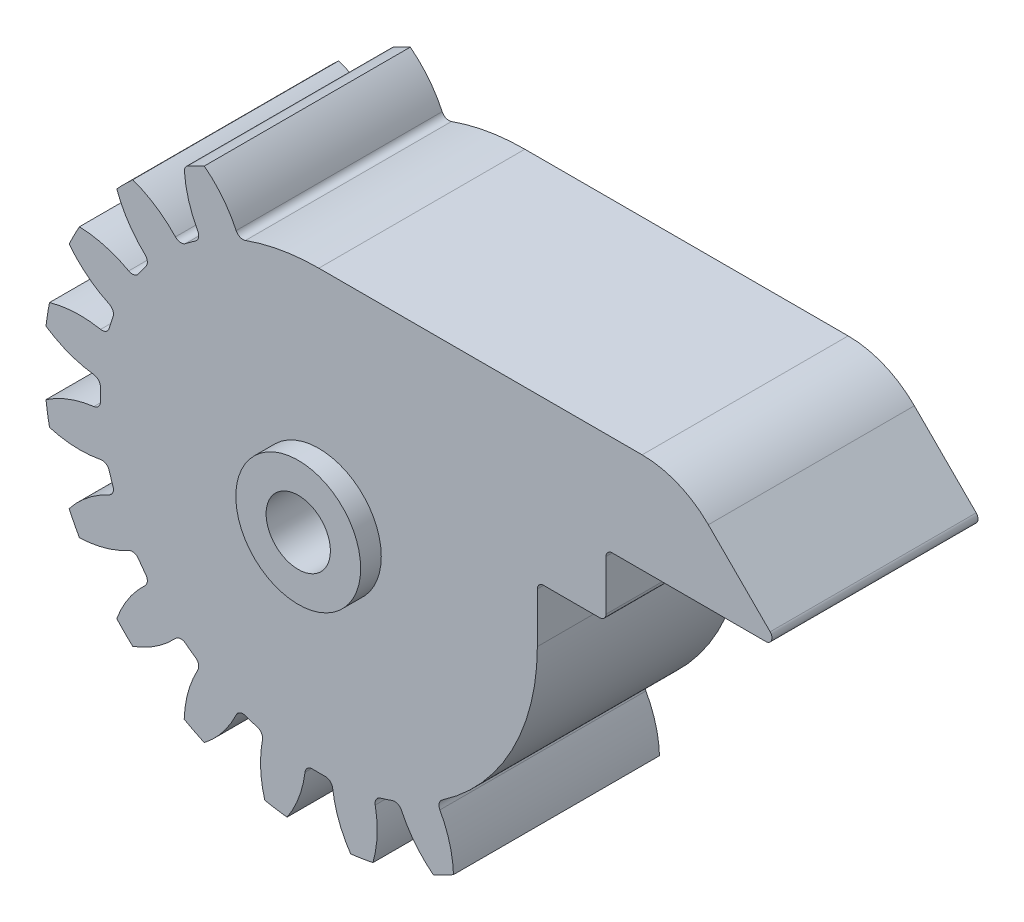
SolidWorks part; units mm, degrees
material "1023 Carbon Steel Sheet (SS)"
ref_plane "Front Plane" through (0, 0, 0) normal (0, 0, 1) x (1, 0, 0)
ref_plane "Top Plane" through (0, 0, 0) normal (0, 1, 0) x (1, 0, 0)
ref_plane "Right Plane" through (0, 0, 0) normal (1, 0, 0) x (0, 0, -1)
sketch "skBase" plane through (0, 0, 0) normal (0, 0, 1) x (1, 0, 0)
  circle A0 centre (0, 0) radius 20
  circle A1 centre (0, 0) radius 22
  circle A2 centre (0, 0) radius 17.5
  dimension "D1" = 40
  dimension "D3" = 4.5
extrude "Base" add sketch "skBase" along normal mid plane 16.5 contours A1
sketch "skToothProfile" plane through (0, 0, 0) normal (0, 0, 1) x (1, 0, 0)
  line L0 (0, 0) -> (0, 22) construction
  line L1 (-1.5692, 19.9383) -> (1.5692, 19.9383) construction
  line L2 (-1.0563, 17.4681) -> (0, 0) construction
  line L3 (0, 15.6271) -> (-2.6287, 22.8493) construction
  line L4 (0, 0) -> (3.4416, 21.7291) construction
  line L5 (1.5692, 19.9383) -> (4.6689, 19.4474) construction
  circle A0 centre (0, 0) radius 22 construction
  arc A1 (-1.0563, 17.4681) -> (-3.258, 22.7681) centre (-9.8105, 16.9387) ccw
  arc A2 (1.0563, 17.4681) -> (3.258, 22.7681) centre (9.8105, 16.9387) cw
  circle A3 centre (0, 0) radius 17.5 construction
  arc A4 (1.0563, 17.4681) -> (-1.0563, 17.4681) centre (0, 0) ccw
  circle A5 centre (0, 0) radius 20 construction
  circle A6 centre (0, 0) radius 22 construction
  circle A7 centre (0, 0) radius 23
  arc A8 (3.258, 22.7681) -> (-3.258, 22.7681) centre (0, 0) ccw
  dimension "D2" = 20
  dimension "D3" = 9
  dimension "D1" = 1
extrude "ToothProfile" cut sketch "skToothProfile" against normal through all and the other way through all
fillet "FilletToothProfile" radius 0.6 2 edges at (1.0563, 17.4681, 0) (-1.0563, 17.4681, 0)
pattern_circular "CirPatternTeeth" count 20 over 360 about axis through (0, 0, 0) along (0, 0, 1) of "ToothProfile", "FilletToothProfile"
sketch "skChaveta" plane through (0, 0, 8.25) normal (0, 0, 1) x (1, 0, 0)
  line L0 (0, 2.575) -> (0, 0) construction
  circle A0 centre (0, 0) radius 2.575
  dimension "D1" = 5.15
extrude "Chaveta" cut sketch "skChaveta" against normal through all
sketch "skRebaixo" plane through (0, 0, 8.25) normal (0, 0, 1) x (1, 0, 0)
  circle A0 centre (0, 0) radius 21.5
  circle A1 centre (0, 0) radius 7.5
  dimension "D1" = 43
  dimension "D2" = 15
sketch "Sketch4" plane through (0, 0, -8.25) normal (0, 0, -1) x (-1, 0, 0)
  circle A0 centre (0, 0) radius 17.5
  arc A5 (-2.5459, 21.8522) -> (-4.3314, 21.5694) centre (0, 0) ccw
  arc A6 (-2.5459, 21.8522) -> (-4.3314, 21.5694) centre (0, 0) ccw
  arc A7 (-18.0189, -1.107) -> (-21.8522, -2.5459) centre (-16.9387, -9.8105) ccw
  arc A8 (-18.0189, -1.107) -> (-21.8522, -2.5459) centre (-16.9387, -9.8105) ccw
  arc A9 (-21.5694, -4.3314) -> (-17.4791, -4.5153) centre (-19.1413, 4.096) ccw
  arc A10 (-21.5694, -4.3314) -> (-17.4791, -4.5153) centre (-19.1413, 4.096) ccw
  arc A127 (-19.996, -9.174) -> (-19.1752, -10.7848) centre (0, 0) ccw
  arc A128 (-19.996, -9.174) -> (-19.1752, -10.7848) centre (0, 0) ccw
  arc A129 (-16.1824, -14.904) -> (-14.904, -16.1824) centre (0, 0) ccw
  arc A130 (-16.1824, -14.904) -> (-14.904, -16.1824) centre (0, 0) ccw
  arc A131 (-10.7848, -19.1752) -> (-9.174, -19.996) centre (0, 0) ccw
  arc A132 (-10.7848, -19.1752) -> (-9.174, -19.996) centre (0, 0) ccw
  arc A133 (-4.3314, -21.5694) -> (-2.5459, -21.8522) centre (0, 0) ccw
  arc A134 (-4.3314, -21.5694) -> (-2.5459, -21.8522) centre (0, 0) ccw
  arc A135 (2.5459, -21.8522) -> (4.3314, -21.5694) centre (0, 0) ccw
  arc A136 (2.5459, -21.8522) -> (4.3314, -21.5694) centre (0, 0) ccw
  arc A137 (9.174, -19.996) -> (10.7848, -19.1752) centre (0, 0) ccw
  arc A138 (9.174, -19.996) -> (10.7848, -19.1752) centre (0, 0) ccw
  arc A139 (14.904, -16.1824) -> (16.1824, -14.904) centre (0, 0) ccw
  arc A140 (14.904, -16.1824) -> (16.1824, -14.904) centre (0, 0) ccw
  arc A141 (19.1752, -10.7848) -> (19.996, -9.174) centre (0, 0) ccw
  arc A142 (19.1752, -10.7848) -> (19.996, -9.174) centre (0, 0) ccw
  arc A143 (21.5694, -4.3314) -> (21.8522, -2.5459) centre (0, 0) ccw
  arc A144 (21.5694, -4.3314) -> (21.8522, -2.5459) centre (0, 0) ccw
  arc A145 (21.8522, 2.5459) -> (21.5694, 4.3314) centre (0, 0) ccw
  arc A146 (21.8522, 2.5459) -> (21.5694, 4.3314) centre (0, 0) ccw
  arc A147 (19.996, 9.174) -> (19.1752, 10.7848) centre (0, 0) ccw
  arc A148 (19.996, 9.174) -> (19.1752, 10.7848) centre (0, 0) ccw
  arc A149 (16.1824, 14.904) -> (14.904, 16.1824) centre (0, 0) ccw
  arc A150 (16.1824, 14.904) -> (14.904, 16.1824) centre (0, 0) ccw
  arc A151 (10.7848, 19.1752) -> (9.174, 19.996) centre (0, 0) ccw
  arc A152 (10.7848, 19.1752) -> (9.174, 19.996) centre (0, 0) ccw
  arc A153 (4.3314, 21.5694) -> (2.5459, 21.8522) centre (0, 0) ccw
  arc A154 (4.3314, 21.5694) -> (2.5459, 21.8522) centre (0, 0) ccw
  arc A155 (-9.174, 19.996) -> (-10.7848, 19.1752) centre (0, 0) ccw
  arc A156 (-9.174, 19.996) -> (-10.7848, 19.1752) centre (0, 0) ccw
  arc A157 (-14.904, 16.1824) -> (-16.1824, 14.904) centre (0, 0) ccw
  arc A158 (-14.904, 16.1824) -> (-16.1824, 14.904) centre (0, 0) ccw
  arc A159 (-19.1752, 10.7848) -> (-19.996, 9.174) centre (0, 0) ccw
  arc A160 (-19.1752, 10.7848) -> (-19.996, 9.174) centre (0, 0) ccw
  arc A161 (-21.5694, 4.3314) -> (-21.8522, 2.5459) centre (0, 0) ccw
  arc A162 (-21.5694, 4.3314) -> (-21.8522, 2.5459) centre (0, 0) ccw
  arc A163 (-4.3314, 21.5694) -> (-4.5153, 17.4791) centre (4.096, 19.1413) ccw
  arc A164 (-4.3314, 21.5694) -> (-4.5153, 17.4791) centre (4.096, 19.1413) ccw
  arc A165 (-4.9352, 16.7897) -> (-4.5153, 17.4791) centre (-5.1044, 17.3653) ccw
  arc A166 (-4.9352, 16.7897) -> (-4.5153, 17.4791) centre (-5.1044, 17.3653) ccw
  arc A167 (-4.9352, 16.7897) -> (-5.8761, 16.484) centre (0, 0) ccw
  arc A168 (-4.9352, 16.7897) -> (-5.8761, 16.484) centre (0, 0) ccw
  arc A169 (-6.621, 16.7949) -> (-5.8761, 16.484) centre (-6.0775, 17.0492) ccw
  arc A170 (-6.621, 16.7949) -> (-5.8761, 16.484) centre (-6.0775, 17.0492) ccw
  arc A171 (-6.621, 16.7949) -> (-9.174, 19.996) centre (-14.5647, 13.0781) ccw
  arc A172 (-6.621, 16.7949) -> (-9.174, 19.996) centre (-14.5647, 13.0781) ccw
  arc A173 (-10.7848, 19.1752) -> (-9.6956, 15.2283) centre (-2.0195, 19.4702) ccw
  arc A174 (-10.7848, 19.1752) -> (-9.6956, 15.2283) centre (-2.0195, 19.4702) ccw
  arc A175 (-9.882, 14.4429) -> (-9.6956, 15.2283) centre (-10.2208, 14.9381) ccw
  arc A176 (-9.882, 14.4429) -> (-9.6956, 15.2283) centre (-10.2208, 14.9381) ccw
  arc A177 (-9.882, 14.4429) -> (-10.6823, 13.8614) centre (0, 0) ccw
  arc A178 (-9.882, 14.4429) -> (-10.6823, 13.8614) centre (0, 0) ccw
  arc A179 (-11.4868, 13.9269) -> (-10.6823, 13.8614) centre (-11.0486, 14.3366) ccw
  arc A180 (-11.4868, 13.9269) -> (-10.6823, 13.8614) centre (-11.0486, 14.3366) ccw
  arc A181 (-11.4868, 13.9269) -> (-14.904, 16.1824) centre (-17.8932, 7.9372) ccw
  arc A182 (-11.4868, 13.9269) -> (-14.904, 16.1824) centre (-17.8932, 7.9372) ccw
  arc A183 (-16.1824, 14.904) -> (-13.9269, 11.4868) centre (-7.9372, 17.8932) ccw
  arc A184 (-16.1824, 14.904) -> (-13.9269, 11.4868) centre (-7.9372, 17.8932) ccw
  arc A185 (-13.8614, 10.6823) -> (-13.9269, 11.4868) centre (-14.3366, 11.0486) ccw
  arc A186 (-13.8614, 10.6823) -> (-13.9269, 11.4868) centre (-14.3366, 11.0486) ccw
  arc A187 (-13.8614, 10.6823) -> (-14.4429, 9.882) centre (0, 0) ccw
  arc A188 (-13.8614, 10.6823) -> (-14.4429, 9.882) centre (0, 0) ccw
  arc A189 (-15.2283, 9.6956) -> (-14.4429, 9.882) centre (-14.9381, 10.2208) ccw
  arc A190 (-15.2283, 9.6956) -> (-14.4429, 9.882) centre (-14.9381, 10.2208) ccw
  arc A191 (-15.2283, 9.6956) -> (-19.1752, 10.7848) centre (-19.4702, 2.0195) ccw
  arc A192 (-15.2283, 9.6956) -> (-19.1752, 10.7848) centre (-19.4702, 2.0195) ccw
  arc A193 (-19.996, 9.174) -> (-16.7949, 6.621) centre (-13.0781, 14.5647) ccw
  arc A194 (-19.996, 9.174) -> (-16.7949, 6.621) centre (-13.0781, 14.5647) ccw
  arc A195 (-16.484, 5.8761) -> (-16.7949, 6.621) centre (-17.0492, 6.0775) ccw
  arc A196 (-16.484, 5.8761) -> (-16.7949, 6.621) centre (-17.0492, 6.0775) ccw
  arc A197 (-16.484, 5.8761) -> (-16.7897, 4.9352) centre (0, 0) ccw
  arc A198 (-16.484, 5.8761) -> (-16.7897, 4.9352) centre (0, 0) ccw
  arc A199 (-17.4791, 4.5153) -> (-16.7897, 4.9352) centre (-17.3653, 5.1044) ccw
  arc A200 (-17.4791, 4.5153) -> (-16.7897, 4.9352) centre (-17.3653, 5.1044) ccw
  arc A201 (-17.4791, 4.5153) -> (-21.5694, 4.3314) centre (-19.1413, -4.096) ccw
  arc A202 (-17.4791, 4.5153) -> (-21.5694, 4.3314) centre (-19.1413, -4.096) ccw
  arc A203 (-21.8522, 2.5459) -> (-18.0189, 1.107) centre (-16.9387, 9.8105) ccw
  arc A204 (-21.8522, 2.5459) -> (-18.0189, 1.107) centre (-16.9387, 9.8105) ccw
  arc A205 (-17.493, 0.4946) -> (-18.0189, 1.107) centre (-18.0928, 0.5116) ccw
  arc A206 (-17.493, 0.4946) -> (-18.0189, 1.107) centre (-18.0928, 0.5116) ccw
  arc A207 (-17.493, 0.4946) -> (-17.493, -0.4946) centre (0, 0) ccw
  arc A208 (-17.493, 0.4946) -> (-17.493, -0.4946) centre (0, 0) ccw
  arc A209 (-18.0189, -1.107) -> (-17.493, -0.4946) centre (-18.0928, -0.5116) ccw
  arc A210 (-18.0189, -1.107) -> (-17.493, -0.4946) centre (-18.0928, -0.5116) ccw
  arc A211 (-16.7897, -4.9352) -> (-17.4791, -4.5153) centre (-17.3653, -5.1044) ccw
  arc A212 (-16.7897, -4.9352) -> (-17.4791, -4.5153) centre (-17.3653, -5.1044) ccw
  arc A213 (-16.7897, -4.9352) -> (-16.484, -5.8761) centre (0, 0) ccw
  arc A214 (-16.7897, -4.9352) -> (-16.484, -5.8761) centre (0, 0) ccw
  arc A215 (-16.7949, -6.621) -> (-16.484, -5.8761) centre (-17.0492, -6.0775) ccw
  arc A216 (-16.7949, -6.621) -> (-16.484, -5.8761) centre (-17.0492, -6.0775) ccw
  arc A217 (-16.7949, -6.621) -> (-19.996, -9.174) centre (-13.0781, -14.5647) ccw
  arc A218 (-16.7949, -6.621) -> (-19.996, -9.174) centre (-13.0781, -14.5647) ccw
  arc A219 (-19.1752, -10.7848) -> (-15.2283, -9.6956) centre (-19.4702, -2.0195) ccw
  arc A220 (-19.1752, -10.7848) -> (-15.2283, -9.6956) centre (-19.4702, -2.0195) ccw
  arc A221 (-14.4429, -9.882) -> (-15.2283, -9.6956) centre (-14.9381, -10.2208) ccw
  arc A222 (-14.4429, -9.882) -> (-15.2283, -9.6956) centre (-14.9381, -10.2208) ccw
  arc A223 (-14.4429, -9.882) -> (-13.8614, -10.6823) centre (0, 0) ccw
  arc A224 (-14.4429, -9.882) -> (-13.8614, -10.6823) centre (0, 0) ccw
  arc A225 (-13.9269, -11.4868) -> (-13.8614, -10.6823) centre (-14.3366, -11.0486) ccw
  arc A226 (-13.9269, -11.4868) -> (-13.8614, -10.6823) centre (-14.3366, -11.0486) ccw
  arc A227 (-13.9269, -11.4868) -> (-16.1824, -14.904) centre (-7.9372, -17.8932) ccw
  arc A228 (-13.9269, -11.4868) -> (-16.1824, -14.904) centre (-7.9372, -17.8932) ccw
  arc A229 (-14.904, -16.1824) -> (-11.4868, -13.9269) centre (-17.8932, -7.9372) ccw
  arc A230 (-14.904, -16.1824) -> (-11.4868, -13.9269) centre (-17.8932, -7.9372) ccw
  arc A231 (-10.6823, -13.8614) -> (-11.4868, -13.9269) centre (-11.0486, -14.3366) ccw
  arc A232 (-10.6823, -13.8614) -> (-11.4868, -13.9269) centre (-11.0486, -14.3366) ccw
  arc A233 (-10.6823, -13.8614) -> (-9.882, -14.4429) centre (0, 0) ccw
  arc A234 (-10.6823, -13.8614) -> (-9.882, -14.4429) centre (0, 0) ccw
  arc A235 (-9.6956, -15.2283) -> (-9.882, -14.4429) centre (-10.2208, -14.9381) ccw
  arc A236 (-9.6956, -15.2283) -> (-9.882, -14.4429) centre (-10.2208, -14.9381) ccw
  arc A237 (-9.6956, -15.2283) -> (-10.7848, -19.1752) centre (-2.0195, -19.4702) ccw
  arc A238 (-9.6956, -15.2283) -> (-10.7848, -19.1752) centre (-2.0195, -19.4702) ccw
  arc A239 (-9.174, -19.996) -> (-6.621, -16.7949) centre (-14.5647, -13.0781) ccw
  arc A240 (-9.174, -19.996) -> (-6.621, -16.7949) centre (-14.5647, -13.0781) ccw
  arc A241 (-5.8761, -16.484) -> (-6.621, -16.7949) centre (-6.0775, -17.0492) ccw
  arc A242 (-5.8761, -16.484) -> (-6.621, -16.7949) centre (-6.0775, -17.0492) ccw
  arc A243 (-5.8761, -16.484) -> (-4.9352, -16.7897) centre (0, 0) ccw
  arc A244 (-5.8761, -16.484) -> (-4.9352, -16.7897) centre (0, 0) ccw
  arc A245 (-4.5153, -17.4791) -> (-4.9352, -16.7897) centre (-5.1044, -17.3653) ccw
  arc A246 (-4.5153, -17.4791) -> (-4.9352, -16.7897) centre (-5.1044, -17.3653) ccw
  arc A247 (-4.5153, -17.4791) -> (-4.3314, -21.5694) centre (4.096, -19.1413) ccw
  arc A248 (-4.5153, -17.4791) -> (-4.3314, -21.5694) centre (4.096, -19.1413) ccw
  arc A249 (-2.5459, -21.8522) -> (-1.107, -18.0189) centre (-9.8105, -16.9387) ccw
  arc A250 (-2.5459, -21.8522) -> (-1.107, -18.0189) centre (-9.8105, -16.9387) ccw
  arc A251 (-0.4946, -17.493) -> (-1.107, -18.0189) centre (-0.5116, -18.0928) ccw
  arc A252 (-0.4946, -17.493) -> (-1.107, -18.0189) centre (-0.5116, -18.0928) ccw
  arc A253 (-0.4946, -17.493) -> (0.4946, -17.493) centre (0, 0) ccw
  arc A254 (-0.4946, -17.493) -> (0.4946, -17.493) centre (0, 0) ccw
  arc A255 (1.107, -18.0189) -> (0.4946, -17.493) centre (0.5116, -18.0928) ccw
  arc A256 (1.107, -18.0189) -> (0.4946, -17.493) centre (0.5116, -18.0928) ccw
  arc A257 (1.107, -18.0189) -> (2.5459, -21.8522) centre (9.8105, -16.9387) ccw
  arc A258 (1.107, -18.0189) -> (2.5459, -21.8522) centre (9.8105, -16.9387) ccw
  arc A259 (4.3314, -21.5694) -> (4.5153, -17.4791) centre (-4.096, -19.1413) ccw
  arc A260 (4.3314, -21.5694) -> (4.5153, -17.4791) centre (-4.096, -19.1413) ccw
  arc A261 (4.9352, -16.7897) -> (4.5153, -17.4791) centre (5.1044, -17.3653) ccw
  arc A262 (4.9352, -16.7897) -> (4.5153, -17.4791) centre (5.1044, -17.3653) ccw
  arc A263 (4.9352, -16.7897) -> (5.8761, -16.484) centre (0, 0) ccw
  arc A264 (4.9352, -16.7897) -> (5.8761, -16.484) centre (0, 0) ccw
  arc A265 (6.621, -16.7949) -> (5.8761, -16.484) centre (6.0775, -17.0492) ccw
  arc A266 (6.621, -16.7949) -> (5.8761, -16.484) centre (6.0775, -17.0492) ccw
  arc A267 (6.621, -16.7949) -> (9.174, -19.996) centre (14.5647, -13.0781) ccw
  arc A268 (6.621, -16.7949) -> (9.174, -19.996) centre (14.5647, -13.0781) ccw
  arc A269 (10.7848, -19.1752) -> (9.6956, -15.2283) centre (2.0195, -19.4702) ccw
  arc A270 (10.7848, -19.1752) -> (9.6956, -15.2283) centre (2.0195, -19.4702) ccw
  arc A271 (9.882, -14.4429) -> (9.6956, -15.2283) centre (10.2208, -14.9381) ccw
  arc A272 (9.882, -14.4429) -> (9.6956, -15.2283) centre (10.2208, -14.9381) ccw
  arc A273 (9.882, -14.4429) -> (10.6823, -13.8614) centre (0, 0) ccw
  arc A274 (9.882, -14.4429) -> (10.6823, -13.8614) centre (0, 0) ccw
  arc A275 (11.4868, -13.9269) -> (10.6823, -13.8614) centre (11.0486, -14.3366) ccw
  arc A276 (11.4868, -13.9269) -> (10.6823, -13.8614) centre (11.0486, -14.3366) ccw
  arc A277 (11.4868, -13.9269) -> (14.904, -16.1824) centre (17.8932, -7.9372) ccw
  arc A278 (11.4868, -13.9269) -> (14.904, -16.1824) centre (17.8932, -7.9372) ccw
  arc A279 (16.1824, -14.904) -> (13.9269, -11.4868) centre (7.9372, -17.8932) ccw
  arc A280 (16.1824, -14.904) -> (13.9269, -11.4868) centre (7.9372, -17.8932) ccw
  arc A281 (13.8614, -10.6823) -> (13.9269, -11.4868) centre (14.3366, -11.0486) ccw
  arc A282 (13.8614, -10.6823) -> (13.9269, -11.4868) centre (14.3366, -11.0486) ccw
  arc A283 (13.8614, -10.6823) -> (14.4429, -9.882) centre (0, 0) ccw
  arc A284 (13.8614, -10.6823) -> (14.4429, -9.882) centre (0, 0) ccw
  arc A285 (15.2283, -9.6956) -> (14.4429, -9.882) centre (14.9381, -10.2208) ccw
  arc A286 (15.2283, -9.6956) -> (14.4429, -9.882) centre (14.9381, -10.2208) ccw
  arc A287 (15.2283, -9.6956) -> (19.1752, -10.7848) centre (19.4702, -2.0195) ccw
  arc A288 (15.2283, -9.6956) -> (19.1752, -10.7848) centre (19.4702, -2.0195) ccw
  arc A289 (19.996, -9.174) -> (16.7949, -6.621) centre (13.0781, -14.5647) ccw
  arc A290 (19.996, -9.174) -> (16.7949, -6.621) centre (13.0781, -14.5647) ccw
  arc A291 (16.484, -5.8761) -> (16.7949, -6.621) centre (17.0492, -6.0775) ccw
  arc A292 (16.484, -5.8761) -> (16.7949, -6.621) centre (17.0492, -6.0775) ccw
  arc A293 (16.484, -5.8761) -> (16.7897, -4.9352) centre (0, 0) ccw
  arc A294 (16.484, -5.8761) -> (16.7897, -4.9352) centre (0, 0) ccw
  arc A295 (17.4791, -4.5153) -> (16.7897, -4.9352) centre (17.3653, -5.1044) ccw
  arc A296 (17.4791, -4.5153) -> (16.7897, -4.9352) centre (17.3653, -5.1044) ccw
  arc A297 (17.4791, -4.5153) -> (21.5694, -4.3314) centre (19.1413, 4.096) ccw
  arc A298 (17.4791, -4.5153) -> (21.5694, -4.3314) centre (19.1413, 4.096) ccw
  arc A299 (21.8522, -2.5459) -> (18.0189, -1.107) centre (16.9387, -9.8105) ccw
  arc A300 (21.8522, -2.5459) -> (18.0189, -1.107) centre (16.9387, -9.8105) ccw
  arc A301 (17.493, -0.4946) -> (18.0189, -1.107) centre (18.0928, -0.5116) ccw
  arc A302 (17.493, -0.4946) -> (18.0189, -1.107) centre (18.0928, -0.5116) ccw
  arc A303 (17.493, -0.4946) -> (17.493, 0.4946) centre (0, 0) ccw
  arc A304 (17.493, -0.4946) -> (17.493, 0.4946) centre (0, 0) ccw
  arc A305 (18.0189, 1.107) -> (17.493, 0.4946) centre (18.0928, 0.5116) ccw
  arc A306 (18.0189, 1.107) -> (17.493, 0.4946) centre (18.0928, 0.5116) ccw
  arc A307 (18.0189, 1.107) -> (21.8522, 2.5459) centre (16.9387, 9.8105) ccw
  arc A308 (18.0189, 1.107) -> (21.8522, 2.5459) centre (16.9387, 9.8105) ccw
  arc A309 (21.5694, 4.3314) -> (17.4791, 4.5153) centre (19.1413, -4.096) ccw
  arc A310 (21.5694, 4.3314) -> (17.4791, 4.5153) centre (19.1413, -4.096) ccw
  arc A311 (-21.8522, -2.5459) -> (-21.5694, -4.3314) centre (0, 0) ccw
  arc A312 (-21.8522, -2.5459) -> (-21.5694, -4.3314) centre (0, 0) ccw
  arc A313 (16.7897, 4.9352) -> (17.4791, 4.5153) centre (17.3653, 5.1044) ccw
  arc A314 (16.7897, 4.9352) -> (17.4791, 4.5153) centre (17.3653, 5.1044) ccw
  arc A315 (16.7897, 4.9352) -> (16.484, 5.8761) centre (0, 0) ccw
  arc A316 (16.7897, 4.9352) -> (16.484, 5.8761) centre (0, 0) ccw
  arc A317 (16.7949, 6.621) -> (16.484, 5.8761) centre (17.0492, 6.0775) ccw
  arc A318 (16.7949, 6.621) -> (16.484, 5.8761) centre (17.0492, 6.0775) ccw
  arc A319 (16.7949, 6.621) -> (19.996, 9.174) centre (13.0781, 14.5647) ccw
  arc A320 (16.7949, 6.621) -> (19.996, 9.174) centre (13.0781, 14.5647) ccw
  arc A321 (19.1752, 10.7848) -> (15.2283, 9.6956) centre (19.4702, 2.0195) ccw
  arc A322 (19.1752, 10.7848) -> (15.2283, 9.6956) centre (19.4702, 2.0195) ccw
  arc A323 (14.4429, 9.882) -> (15.2283, 9.6956) centre (14.9381, 10.2208) ccw
  arc A324 (14.4429, 9.882) -> (15.2283, 9.6956) centre (14.9381, 10.2208) ccw
  arc A325 (14.4429, 9.882) -> (13.8614, 10.6823) centre (0, 0) ccw
  arc A326 (14.4429, 9.882) -> (13.8614, 10.6823) centre (0, 0) ccw
  arc A327 (13.9269, 11.4868) -> (13.8614, 10.6823) centre (14.3366, 11.0486) ccw
  arc A328 (13.9269, 11.4868) -> (13.8614, 10.6823) centre (14.3366, 11.0486) ccw
  arc A329 (13.9269, 11.4868) -> (16.1824, 14.904) centre (7.9372, 17.8932) ccw
  arc A330 (13.9269, 11.4868) -> (16.1824, 14.904) centre (7.9372, 17.8932) ccw
  arc A331 (14.904, 16.1824) -> (11.4868, 13.9269) centre (17.8932, 7.9372) ccw
  arc A332 (14.904, 16.1824) -> (11.4868, 13.9269) centre (17.8932, 7.9372) ccw
  arc A333 (10.6823, 13.8614) -> (11.4868, 13.9269) centre (11.0486, 14.3366) ccw
  arc A334 (10.6823, 13.8614) -> (11.4868, 13.9269) centre (11.0486, 14.3366) ccw
  arc A335 (10.6823, 13.8614) -> (9.882, 14.4429) centre (0, 0) ccw
  arc A336 (10.6823, 13.8614) -> (9.882, 14.4429) centre (0, 0) ccw
  arc A337 (9.6956, 15.2283) -> (9.882, 14.4429) centre (10.2208, 14.9381) ccw
  arc A338 (9.6956, 15.2283) -> (9.882, 14.4429) centre (10.2208, 14.9381) ccw
  arc A339 (9.6956, 15.2283) -> (10.7848, 19.1752) centre (2.0195, 19.4702) ccw
  arc A340 (9.6956, 15.2283) -> (10.7848, 19.1752) centre (2.0195, 19.4702) ccw
  arc A341 (9.174, 19.996) -> (6.621, 16.7949) centre (14.5647, 13.0781) ccw
  arc A342 (9.174, 19.996) -> (6.621, 16.7949) centre (14.5647, 13.0781) ccw
  arc A343 (5.8761, 16.484) -> (6.621, 16.7949) centre (6.0775, 17.0492) ccw
  arc A344 (5.8761, 16.484) -> (6.621, 16.7949) centre (6.0775, 17.0492) ccw
  arc A345 (5.8761, 16.484) -> (4.9352, 16.7897) centre (0, 0) ccw
  arc A346 (5.8761, 16.484) -> (4.9352, 16.7897) centre (0, 0) ccw
  arc A347 (4.5153, 17.4791) -> (4.9352, 16.7897) centre (5.1044, 17.3653) ccw
  arc A348 (4.5153, 17.4791) -> (4.9352, 16.7897) centre (5.1044, 17.3653) ccw
  arc A349 (4.5153, 17.4791) -> (4.3314, 21.5694) centre (-4.096, 19.1413) ccw
  arc A350 (4.5153, 17.4791) -> (4.3314, 21.5694) centre (-4.096, 19.1413) ccw
  arc A351 (2.5459, 21.8522) -> (1.107, 18.0189) centre (9.8105, 16.9387) ccw
  arc A352 (2.5459, 21.8522) -> (1.107, 18.0189) centre (9.8105, 16.9387) ccw
  arc A353 (0.4946, 17.493) -> (1.107, 18.0189) centre (0.5116, 18.0928) ccw
  arc A354 (0.4946, 17.493) -> (1.107, 18.0189) centre (0.5116, 18.0928) ccw
  arc A355 (0.4946, 17.493) -> (-0.4946, 17.493) centre (0, 0) ccw
  arc A356 (0.4946, 17.493) -> (-0.4946, 17.493) centre (0, 0) ccw
  arc A357 (-1.107, 18.0189) -> (-0.4946, 17.493) centre (-0.5116, 18.0928) ccw
  arc A358 (-1.107, 18.0189) -> (-0.4946, 17.493) centre (-0.5116, 18.0928) ccw
  arc A359 (-1.107, 18.0189) -> (-2.5459, 21.8522) centre (-9.8105, 16.9387) ccw
  arc A360 (-1.107, 18.0189) -> (-2.5459, 21.8522) centre (-9.8105, 16.9387) ccw
  dimension "D1" = 0
sketch "Sketch6" plane through (0, 0, -8.25) normal (0, 0, -1) x (-1, 0, 0)
  circle A0 centre (0, 0) radius 20 construction
  dimension "D1" = 40
sketch "Sketch7" plane through (0, 0, -8.25) normal (0, 0, -1) x (-1, 0, 0)
  circle A0 centre (0, 0) radius 17.5
  arc A120 (-2.5459, 21.8522) -> (-4.3314, 21.5694) centre (0, 0) ccw
  arc A121 (-4.3314, 21.5694) -> (-4.5153, 17.4791) centre (4.096, 19.1413) ccw
  arc A122 (-4.9352, 16.7897) -> (-4.5153, 17.4791) centre (-5.1044, 17.3653) ccw
  arc A123 (-4.9352, 16.7897) -> (-5.8761, 16.484) centre (0, 0) ccw
  arc A124 (-6.621, 16.7949) -> (-5.8761, 16.484) centre (-6.0775, 17.0492) ccw
  arc A125 (-6.621, 16.7949) -> (-9.174, 19.996) centre (-14.5647, 13.0781) ccw
  arc A126 (-9.174, 19.996) -> (-10.7848, 19.1752) centre (0, 0) ccw
  arc A127 (-10.7848, 19.1752) -> (-9.6956, 15.2283) centre (-2.0195, 19.4702) ccw
  arc A128 (-9.882, 14.4429) -> (-9.6956, 15.2283) centre (-10.2208, 14.9381) ccw
  arc A129 (-9.882, 14.4429) -> (-10.6823, 13.8614) centre (0, 0) ccw
  arc A130 (-11.4868, 13.9269) -> (-10.6823, 13.8614) centre (-11.0486, 14.3366) ccw
  arc A131 (-11.4868, 13.9269) -> (-14.904, 16.1824) centre (-17.8932, 7.9372) ccw
  arc A132 (-14.904, 16.1824) -> (-16.1824, 14.904) centre (0, 0) ccw
  arc A133 (-16.1824, 14.904) -> (-13.9269, 11.4868) centre (-7.9372, 17.8932) ccw
  arc A134 (-13.8614, 10.6823) -> (-13.9269, 11.4868) centre (-14.3366, 11.0486) ccw
  arc A135 (-13.8614, 10.6823) -> (-14.4429, 9.882) centre (0, 0) ccw
  arc A136 (-15.2283, 9.6956) -> (-14.4429, 9.882) centre (-14.9381, 10.2208) ccw
  arc A137 (-15.2283, 9.6956) -> (-19.1752, 10.7848) centre (-19.4702, 2.0195) ccw
  arc A138 (-19.1752, 10.7848) -> (-19.996, 9.174) centre (0, 0) ccw
  arc A139 (-19.996, 9.174) -> (-16.7949, 6.621) centre (-13.0781, 14.5647) ccw
  arc A140 (-16.484, 5.8761) -> (-16.7949, 6.621) centre (-17.0492, 6.0775) ccw
  arc A141 (-16.484, 5.8761) -> (-16.7897, 4.9352) centre (0, 0) ccw
  arc A142 (-17.4791, 4.5153) -> (-16.7897, 4.9352) centre (-17.3653, 5.1044) ccw
  arc A143 (-17.4791, 4.5153) -> (-21.5694, 4.3314) centre (-19.1413, -4.096) ccw
  arc A144 (-21.5694, 4.3314) -> (-21.8522, 2.5459) centre (0, 0) ccw
  arc A145 (-21.8522, 2.5459) -> (-18.0189, 1.107) centre (-16.9387, 9.8105) ccw
  arc A146 (-17.493, 0.4946) -> (-18.0189, 1.107) centre (-18.0928, 0.5116) ccw
  arc A147 (-17.493, 0.4946) -> (-17.493, -0.4946) centre (0, 0) ccw
  arc A148 (-18.0189, -1.107) -> (-17.493, -0.4946) centre (-18.0928, -0.5116) ccw
  arc A149 (-18.0189, -1.107) -> (-21.8522, -2.5459) centre (-16.9387, -9.8105) ccw
  arc A150 (-21.8522, -2.5459) -> (-21.5694, -4.3314) centre (0, 0) ccw
  arc A151 (-21.5694, -4.3314) -> (-17.4791, -4.5153) centre (-19.1413, 4.096) ccw
  arc A152 (-16.7897, -4.9352) -> (-17.4791, -4.5153) centre (-17.3653, -5.1044) ccw
  arc A153 (-16.7897, -4.9352) -> (-16.484, -5.8761) centre (0, 0) ccw
  arc A154 (-16.7949, -6.621) -> (-16.484, -5.8761) centre (-17.0492, -6.0775) ccw
  arc A155 (-16.7949, -6.621) -> (-19.996, -9.174) centre (-13.0781, -14.5647) ccw
  arc A156 (-19.996, -9.174) -> (-19.1752, -10.7848) centre (0, 0) ccw
  arc A157 (-19.1752, -10.7848) -> (-15.2283, -9.6956) centre (-19.4702, -2.0195) ccw
  arc A158 (-14.4429, -9.882) -> (-15.2283, -9.6956) centre (-14.9381, -10.2208) ccw
  arc A159 (-14.4429, -9.882) -> (-13.8614, -10.6823) centre (0, 0) ccw
  arc A160 (-13.9269, -11.4868) -> (-13.8614, -10.6823) centre (-14.3366, -11.0486) ccw
  arc A161 (-13.9269, -11.4868) -> (-16.1824, -14.904) centre (-7.9372, -17.8932) ccw
  arc A162 (-16.1824, -14.904) -> (-14.904, -16.1824) centre (0, 0) ccw
  arc A163 (-14.904, -16.1824) -> (-11.4868, -13.9269) centre (-17.8932, -7.9372) ccw
  arc A164 (-10.6823, -13.8614) -> (-11.4868, -13.9269) centre (-11.0486, -14.3366) ccw
  arc A165 (-10.6823, -13.8614) -> (-9.882, -14.4429) centre (0, 0) ccw
  arc A166 (-9.6956, -15.2283) -> (-9.882, -14.4429) centre (-10.2208, -14.9381) ccw
  arc A167 (-9.6956, -15.2283) -> (-10.7848, -19.1752) centre (-2.0195, -19.4702) ccw
  arc A168 (-10.7848, -19.1752) -> (-9.174, -19.996) centre (0, 0) ccw
  arc A169 (-9.174, -19.996) -> (-6.621, -16.7949) centre (-14.5647, -13.0781) ccw
  arc A170 (-5.8761, -16.484) -> (-6.621, -16.7949) centre (-6.0775, -17.0492) ccw
  arc A171 (-5.8761, -16.484) -> (-4.9352, -16.7897) centre (0, 0) ccw
  arc A172 (-4.5153, -17.4791) -> (-4.9352, -16.7897) centre (-5.1044, -17.3653) ccw
  arc A173 (-4.5153, -17.4791) -> (-4.3314, -21.5694) centre (4.096, -19.1413) ccw
  arc A174 (-4.3314, -21.5694) -> (-2.5459, -21.8522) centre (0, 0) ccw
  arc A175 (-2.5459, -21.8522) -> (-1.107, -18.0189) centre (-9.8105, -16.9387) ccw
  arc A176 (-0.4946, -17.493) -> (-1.107, -18.0189) centre (-0.5116, -18.0928) ccw
  arc A177 (-0.4946, -17.493) -> (0.4946, -17.493) centre (0, 0) ccw
  arc A178 (1.107, -18.0189) -> (0.4946, -17.493) centre (0.5116, -18.0928) ccw
  arc A179 (1.107, -18.0189) -> (2.5459, -21.8522) centre (9.8105, -16.9387) ccw
  arc A180 (2.5459, -21.8522) -> (4.3314, -21.5694) centre (0, 0) ccw
  arc A181 (4.3314, -21.5694) -> (4.5153, -17.4791) centre (-4.096, -19.1413) ccw
  arc A182 (4.9352, -16.7897) -> (4.5153, -17.4791) centre (5.1044, -17.3653) ccw
  arc A183 (4.9352, -16.7897) -> (5.8761, -16.484) centre (0, 0) ccw
  arc A184 (6.621, -16.7949) -> (5.8761, -16.484) centre (6.0775, -17.0492) ccw
  arc A185 (6.621, -16.7949) -> (9.174, -19.996) centre (14.5647, -13.0781) ccw
  arc A186 (9.174, -19.996) -> (10.7848, -19.1752) centre (0, 0) ccw
  arc A187 (10.7848, -19.1752) -> (9.6956, -15.2283) centre (2.0195, -19.4702) ccw
  arc A188 (9.882, -14.4429) -> (9.6956, -15.2283) centre (10.2208, -14.9381) ccw
  arc A189 (9.882, -14.4429) -> (10.6823, -13.8614) centre (0, 0) ccw
  arc A190 (11.4868, -13.9269) -> (10.6823, -13.8614) centre (11.0486, -14.3366) ccw
  arc A191 (11.4868, -13.9269) -> (14.904, -16.1824) centre (17.8932, -7.9372) ccw
  arc A192 (14.904, -16.1824) -> (16.1824, -14.904) centre (0, 0) ccw
  arc A193 (16.1824, -14.904) -> (13.9269, -11.4868) centre (7.9372, -17.8932) ccw
  arc A194 (13.8614, -10.6823) -> (13.9269, -11.4868) centre (14.3366, -11.0486) ccw
  arc A195 (13.8614, -10.6823) -> (14.4429, -9.882) centre (0, 0) ccw
  arc A196 (15.2283, -9.6956) -> (14.4429, -9.882) centre (14.9381, -10.2208) ccw
  arc A197 (15.2283, -9.6956) -> (19.1752, -10.7848) centre (19.4702, -2.0195) ccw
  arc A198 (19.1752, -10.7848) -> (19.996, -9.174) centre (0, 0) ccw
  arc A199 (19.996, -9.174) -> (16.7949, -6.621) centre (13.0781, -14.5647) ccw
  arc A200 (16.484, -5.8761) -> (16.7949, -6.621) centre (17.0492, -6.0775) ccw
  arc A201 (16.484, -5.8761) -> (16.7897, -4.9352) centre (0, 0) ccw
  arc A202 (17.4791, -4.5153) -> (16.7897, -4.9352) centre (17.3653, -5.1044) ccw
  arc A203 (17.4791, -4.5153) -> (21.5694, -4.3314) centre (19.1413, 4.096) ccw
  arc A204 (21.5694, -4.3314) -> (21.8522, -2.5459) centre (0, 0) ccw
  arc A205 (21.8522, -2.5459) -> (18.0189, -1.107) centre (16.9387, -9.8105) ccw
  arc A206 (17.493, -0.4946) -> (18.0189, -1.107) centre (18.0928, -0.5116) ccw
  arc A207 (17.493, -0.4946) -> (17.493, 0.4946) centre (0, 0) ccw
  arc A208 (18.0189, 1.107) -> (17.493, 0.4946) centre (18.0928, 0.5116) ccw
  arc A209 (18.0189, 1.107) -> (21.8522, 2.5459) centre (16.9387, 9.8105) ccw
  arc A210 (21.8522, 2.5459) -> (21.5694, 4.3314) centre (0, 0) ccw
  arc A211 (21.5694, 4.3314) -> (17.4791, 4.5153) centre (19.1413, -4.096) ccw
  arc A212 (16.7897, 4.9352) -> (17.4791, 4.5153) centre (17.3653, 5.1044) ccw
  arc A213 (16.7897, 4.9352) -> (16.484, 5.8761) centre (0, 0) ccw
  arc A214 (16.7949, 6.621) -> (16.484, 5.8761) centre (17.0492, 6.0775) ccw
  arc A215 (16.7949, 6.621) -> (19.996, 9.174) centre (13.0781, 14.5647) ccw
  arc A216 (19.996, 9.174) -> (19.1752, 10.7848) centre (0, 0) ccw
  arc A217 (19.1752, 10.7848) -> (15.2283, 9.6956) centre (19.4702, 2.0195) ccw
  arc A218 (14.4429, 9.882) -> (15.2283, 9.6956) centre (14.9381, 10.2208) ccw
  arc A219 (14.4429, 9.882) -> (13.8614, 10.6823) centre (0, 0) ccw
  arc A220 (13.9269, 11.4868) -> (13.8614, 10.6823) centre (14.3366, 11.0486) ccw
  arc A221 (13.9269, 11.4868) -> (16.1824, 14.904) centre (7.9372, 17.8932) ccw
  arc A222 (16.1824, 14.904) -> (14.904, 16.1824) centre (0, 0) ccw
  arc A223 (14.904, 16.1824) -> (11.4868, 13.9269) centre (17.8932, 7.9372) ccw
  arc A224 (10.6823, 13.8614) -> (11.4868, 13.9269) centre (11.0486, 14.3366) ccw
  arc A225 (10.6823, 13.8614) -> (9.882, 14.4429) centre (0, 0) ccw
  arc A226 (9.6956, 15.2283) -> (9.882, 14.4429) centre (10.2208, 14.9381) ccw
  arc A227 (9.6956, 15.2283) -> (10.7848, 19.1752) centre (2.0195, 19.4702) ccw
  arc A228 (10.7848, 19.1752) -> (9.174, 19.996) centre (0, 0) ccw
  arc A229 (9.174, 19.996) -> (6.621, 16.7949) centre (14.5647, 13.0781) ccw
  arc A230 (5.8761, 16.484) -> (6.621, 16.7949) centre (6.0775, 17.0492) ccw
  arc A231 (5.8761, 16.484) -> (4.9352, 16.7897) centre (0, 0) ccw
  arc A232 (4.5153, 17.4791) -> (4.9352, 16.7897) centre (5.1044, 17.3653) ccw
  arc A233 (4.5153, 17.4791) -> (4.3314, 21.5694) centre (-4.096, 19.1413) ccw
  arc A234 (4.3314, 21.5694) -> (2.5459, 21.8522) centre (0, 0) ccw
  arc A235 (2.5459, 21.8522) -> (1.107, 18.0189) centre (9.8105, 16.9387) ccw
  arc A236 (0.4946, 17.493) -> (1.107, 18.0189) centre (0.5116, 18.0928) ccw
  arc A237 (0.4946, 17.493) -> (-0.4946, 17.493) centre (0, 0) ccw
  arc A238 (-1.107, 18.0189) -> (-0.4946, 17.493) centre (-0.5116, 18.0928) ccw
  arc A239 (-1.107, 18.0189) -> (-2.5459, 21.8522) centre (-9.8105, 16.9387) ccw
  arc A240 (-2.5459, 21.8522) -> (-4.3314, 21.5694) centre (0, 0) ccw
  arc A241 (-4.3314, 21.5694) -> (-4.5153, 17.4791) centre (4.096, 19.1413) ccw
  arc A242 (-4.9352, 16.7897) -> (-4.5153, 17.4791) centre (-5.1044, 17.3653) ccw
  arc A243 (-4.9352, 16.7897) -> (-5.8761, 16.484) centre (0, 0) ccw
  arc A244 (-6.621, 16.7949) -> (-5.8761, 16.484) centre (-6.0775, 17.0492) ccw
  arc A245 (-6.621, 16.7949) -> (-9.174, 19.996) centre (-14.5647, 13.0781) ccw
  arc A246 (-9.174, 19.996) -> (-10.7848, 19.1752) centre (0, 0) ccw
  arc A247 (-10.7848, 19.1752) -> (-9.6956, 15.2283) centre (-2.0195, 19.4702) ccw
  arc A248 (-9.882, 14.4429) -> (-9.6956, 15.2283) centre (-10.2208, 14.9381) ccw
  arc A249 (-9.882, 14.4429) -> (-10.6823, 13.8614) centre (0, 0) ccw
  arc A250 (-11.4868, 13.9269) -> (-10.6823, 13.8614) centre (-11.0486, 14.3366) ccw
  arc A251 (-11.4868, 13.9269) -> (-14.904, 16.1824) centre (-17.8932, 7.9372) ccw
  arc A252 (-14.904, 16.1824) -> (-16.1824, 14.904) centre (0, 0) ccw
  arc A253 (-16.1824, 14.904) -> (-13.9269, 11.4868) centre (-7.9372, 17.8932) ccw
  arc A254 (-13.8614, 10.6823) -> (-13.9269, 11.4868) centre (-14.3366, 11.0486) ccw
  arc A255 (-13.8614, 10.6823) -> (-14.4429, 9.882) centre (0, 0) ccw
  arc A256 (-15.2283, 9.6956) -> (-14.4429, 9.882) centre (-14.9381, 10.2208) ccw
  arc A257 (-15.2283, 9.6956) -> (-19.1752, 10.7848) centre (-19.4702, 2.0195) ccw
  arc A258 (-19.1752, 10.7848) -> (-19.996, 9.174) centre (0, 0) ccw
  arc A259 (-19.996, 9.174) -> (-16.7949, 6.621) centre (-13.0781, 14.5647) ccw
  arc A260 (-16.484, 5.8761) -> (-16.7949, 6.621) centre (-17.0492, 6.0775) ccw
  arc A261 (-16.484, 5.8761) -> (-16.7897, 4.9352) centre (0, 0) ccw
  arc A262 (-17.4791, 4.5153) -> (-16.7897, 4.9352) centre (-17.3653, 5.1044) ccw
  arc A263 (-17.4791, 4.5153) -> (-21.5694, 4.3314) centre (-19.1413, -4.096) ccw
  arc A264 (-21.5694, 4.3314) -> (-21.8522, 2.5459) centre (0, 0) ccw
  arc A265 (-21.8522, 2.5459) -> (-18.0189, 1.107) centre (-16.9387, 9.8105) ccw
  arc A266 (-17.493, 0.4946) -> (-18.0189, 1.107) centre (-18.0928, 0.5116) ccw
  arc A267 (-17.493, 0.4946) -> (-17.493, -0.4946) centre (0, 0) ccw
  arc A268 (-18.0189, -1.107) -> (-17.493, -0.4946) centre (-18.0928, -0.5116) ccw
  arc A269 (-18.0189, -1.107) -> (-21.8522, -2.5459) centre (-16.9387, -9.8105) ccw
  arc A270 (-21.8522, -2.5459) -> (-21.5694, -4.3314) centre (0, 0) ccw
  arc A271 (-21.5694, -4.3314) -> (-17.4791, -4.5153) centre (-19.1413, 4.096) ccw
  arc A272 (-16.7897, -4.9352) -> (-17.4791, -4.5153) centre (-17.3653, -5.1044) ccw
  arc A273 (-16.7897, -4.9352) -> (-16.484, -5.8761) centre (0, 0) ccw
  arc A274 (-16.7949, -6.621) -> (-16.484, -5.8761) centre (-17.0492, -6.0775) ccw
  arc A275 (-16.7949, -6.621) -> (-19.996, -9.174) centre (-13.0781, -14.5647) ccw
  arc A276 (-19.996, -9.174) -> (-19.1752, -10.7848) centre (0, 0) ccw
  arc A277 (-19.1752, -10.7848) -> (-15.2283, -9.6956) centre (-19.4702, -2.0195) ccw
  arc A278 (-14.4429, -9.882) -> (-15.2283, -9.6956) centre (-14.9381, -10.2208) ccw
  arc A279 (-14.4429, -9.882) -> (-13.8614, -10.6823) centre (0, 0) ccw
  arc A280 (-13.9269, -11.4868) -> (-13.8614, -10.6823) centre (-14.3366, -11.0486) ccw
  arc A281 (-13.9269, -11.4868) -> (-16.1824, -14.904) centre (-7.9372, -17.8932) ccw
  arc A282 (-16.1824, -14.904) -> (-14.904, -16.1824) centre (0, 0) ccw
  arc A283 (-14.904, -16.1824) -> (-11.4868, -13.9269) centre (-17.8932, -7.9372) ccw
  arc A284 (-10.6823, -13.8614) -> (-11.4868, -13.9269) centre (-11.0486, -14.3366) ccw
  arc A285 (-10.6823, -13.8614) -> (-9.882, -14.4429) centre (0, 0) ccw
  arc A286 (-9.6956, -15.2283) -> (-9.882, -14.4429) centre (-10.2208, -14.9381) ccw
  arc A287 (-9.6956, -15.2283) -> (-10.7848, -19.1752) centre (-2.0195, -19.4702) ccw
  arc A288 (-10.7848, -19.1752) -> (-9.174, -19.996) centre (0, 0) ccw
  arc A289 (-9.174, -19.996) -> (-6.621, -16.7949) centre (-14.5647, -13.0781) ccw
  arc A290 (-5.8761, -16.484) -> (-6.621, -16.7949) centre (-6.0775, -17.0492) ccw
  arc A291 (-5.8761, -16.484) -> (-4.9352, -16.7897) centre (0, 0) ccw
  arc A292 (-4.5153, -17.4791) -> (-4.9352, -16.7897) centre (-5.1044, -17.3653) ccw
  arc A293 (-4.5153, -17.4791) -> (-4.3314, -21.5694) centre (4.096, -19.1413) ccw
  arc A294 (-4.3314, -21.5694) -> (-2.5459, -21.8522) centre (0, 0) ccw
  arc A295 (-2.5459, -21.8522) -> (-1.107, -18.0189) centre (-9.8105, -16.9387) ccw
  arc A296 (-0.4946, -17.493) -> (-1.107, -18.0189) centre (-0.5116, -18.0928) ccw
  arc A297 (-0.4946, -17.493) -> (0.4946, -17.493) centre (0, 0) ccw
  arc A298 (1.107, -18.0189) -> (0.4946, -17.493) centre (0.5116, -18.0928) ccw
  arc A299 (1.107, -18.0189) -> (2.5459, -21.8522) centre (9.8105, -16.9387) ccw
  arc A300 (2.5459, -21.8522) -> (4.3314, -21.5694) centre (0, 0) ccw
  arc A301 (4.3314, -21.5694) -> (4.5153, -17.4791) centre (-4.096, -19.1413) ccw
  arc A302 (4.9352, -16.7897) -> (4.5153, -17.4791) centre (5.1044, -17.3653) ccw
  arc A303 (4.9352, -16.7897) -> (5.8761, -16.484) centre (0, 0) ccw
  arc A304 (6.621, -16.7949) -> (5.8761, -16.484) centre (6.0775, -17.0492) ccw
  arc A305 (6.621, -16.7949) -> (9.174, -19.996) centre (14.5647, -13.0781) ccw
  arc A306 (9.174, -19.996) -> (10.7848, -19.1752) centre (0, 0) ccw
  arc A307 (10.7848, -19.1752) -> (9.6956, -15.2283) centre (2.0195, -19.4702) ccw
  arc A308 (9.882, -14.4429) -> (9.6956, -15.2283) centre (10.2208, -14.9381) ccw
  arc A309 (9.882, -14.4429) -> (10.6823, -13.8614) centre (0, 0) ccw
  arc A310 (11.4868, -13.9269) -> (10.6823, -13.8614) centre (11.0486, -14.3366) ccw
  arc A311 (11.4868, -13.9269) -> (14.904, -16.1824) centre (17.8932, -7.9372) ccw
  arc A312 (14.904, -16.1824) -> (16.1824, -14.904) centre (0, 0) ccw
  arc A313 (16.1824, -14.904) -> (13.9269, -11.4868) centre (7.9372, -17.8932) ccw
  arc A314 (13.8614, -10.6823) -> (13.9269, -11.4868) centre (14.3366, -11.0486) ccw
  arc A315 (13.8614, -10.6823) -> (14.4429, -9.882) centre (0, 0) ccw
  arc A316 (15.2283, -9.6956) -> (14.4429, -9.882) centre (14.9381, -10.2208) ccw
  arc A317 (15.2283, -9.6956) -> (19.1752, -10.7848) centre (19.4702, -2.0195) ccw
  arc A318 (19.1752, -10.7848) -> (19.996, -9.174) centre (0, 0) ccw
  arc A319 (19.996, -9.174) -> (16.7949, -6.621) centre (13.0781, -14.5647) ccw
  arc A320 (16.484, -5.8761) -> (16.7949, -6.621) centre (17.0492, -6.0775) ccw
  arc A321 (16.484, -5.8761) -> (16.7897, -4.9352) centre (0, 0) ccw
  arc A322 (17.4791, -4.5153) -> (16.7897, -4.9352) centre (17.3653, -5.1044) ccw
  arc A323 (17.4791, -4.5153) -> (21.5694, -4.3314) centre (19.1413, 4.096) ccw
  arc A324 (21.5694, -4.3314) -> (21.8522, -2.5459) centre (0, 0) ccw
  arc A325 (21.8522, -2.5459) -> (18.0189, -1.107) centre (16.9387, -9.8105) ccw
  arc A326 (17.493, -0.4946) -> (18.0189, -1.107) centre (18.0928, -0.5116) ccw
  arc A327 (17.493, -0.4946) -> (17.493, 0.4946) centre (0, 0) ccw
  arc A328 (18.0189, 1.107) -> (17.493, 0.4946) centre (18.0928, 0.5116) ccw
  arc A329 (18.0189, 1.107) -> (21.8522, 2.5459) centre (16.9387, 9.8105) ccw
  arc A330 (21.8522, 2.5459) -> (21.5694, 4.3314) centre (0, 0) ccw
  arc A331 (21.5694, 4.3314) -> (17.4791, 4.5153) centre (19.1413, -4.096) ccw
  arc A332 (16.7897, 4.9352) -> (17.4791, 4.5153) centre (17.3653, 5.1044) ccw
  arc A333 (16.7897, 4.9352) -> (16.484, 5.8761) centre (0, 0) ccw
  arc A334 (16.7949, 6.621) -> (16.484, 5.8761) centre (17.0492, 6.0775) ccw
  arc A335 (16.7949, 6.621) -> (19.996, 9.174) centre (13.0781, 14.5647) ccw
  arc A336 (19.996, 9.174) -> (19.1752, 10.7848) centre (0, 0) ccw
  arc A337 (19.1752, 10.7848) -> (15.2283, 9.6956) centre (19.4702, 2.0195) ccw
  arc A338 (14.4429, 9.882) -> (15.2283, 9.6956) centre (14.9381, 10.2208) ccw
  arc A339 (14.4429, 9.882) -> (13.8614, 10.6823) centre (0, 0) ccw
  arc A340 (13.9269, 11.4868) -> (13.8614, 10.6823) centre (14.3366, 11.0486) ccw
  arc A341 (13.9269, 11.4868) -> (16.1824, 14.904) centre (7.9372, 17.8932) ccw
  arc A342 (16.1824, 14.904) -> (14.904, 16.1824) centre (0, 0) ccw
  arc A343 (14.904, 16.1824) -> (11.4868, 13.9269) centre (17.8932, 7.9372) ccw
  arc A344 (10.6823, 13.8614) -> (11.4868, 13.9269) centre (11.0486, 14.3366) ccw
  arc A345 (10.6823, 13.8614) -> (9.882, 14.4429) centre (0, 0) ccw
  arc A346 (9.6956, 15.2283) -> (9.882, 14.4429) centre (10.2208, 14.9381) ccw
  arc A347 (9.6956, 15.2283) -> (10.7848, 19.1752) centre (2.0195, 19.4702) ccw
  arc A348 (10.7848, 19.1752) -> (9.174, 19.996) centre (0, 0) ccw
  arc A349 (9.174, 19.996) -> (6.621, 16.7949) centre (14.5647, 13.0781) ccw
  arc A350 (5.8761, 16.484) -> (6.621, 16.7949) centre (6.0775, 17.0492) ccw
  arc A351 (5.8761, 16.484) -> (4.9352, 16.7897) centre (0, 0) ccw
  arc A352 (4.5153, 17.4791) -> (4.9352, 16.7897) centre (5.1044, 17.3653) ccw
  arc A353 (4.5153, 17.4791) -> (4.3314, 21.5694) centre (-4.096, 19.1413) ccw
  arc A354 (4.3314, 21.5694) -> (2.5459, 21.8522) centre (0, 0) ccw
  arc A355 (2.5459, 21.8522) -> (1.107, 18.0189) centre (9.8105, 16.9387) ccw
  arc A356 (0.4946, 17.493) -> (1.107, 18.0189) centre (0.5116, 18.0928) ccw
  arc A357 (0.4946, 17.493) -> (-0.4946, 17.493) centre (0, 0) ccw
  arc A358 (-1.107, 18.0189) -> (-0.4946, 17.493) centre (-0.5116, 18.0928) ccw
  arc A359 (-1.107, 18.0189) -> (-2.5459, 21.8522) centre (-9.8105, 16.9387) ccw
  dimension "D1" = 0
extrude "Cut-Extrude1" cut sketch "Sketch7" against normal blind 16.5 contours A266 A0 A262 A263 A264 A265 | A272 A0 A268 A269 A270 A271 | A278 A0 A274 A275 A276 A277 | A260 A0 A256 A257 A258 A259 | A254 A0 A250 A251 A252 A253 | A248 A0 A244 A245 A246 A247 | A358 A359 A240 A241 A242 A0 | A284 A0 A280 A281 A282 A283 | A356 A0 A352 A353 A354 A355
sketch "Sketch8" plane through (0, 0, -8.25) normal (0, 0, -1) x (-1, 0, 0)
  line L1 (-17.5, 7.125) -> (-2.575, 7.125)
  line L2 (-17.5, 7.125) -> (-17.5, -7.125)
  line L3 (-17.5, -7.125) -> (-2.575, -7.125)
  line L4 (-2.575, 7.125) -> (-2.575, -7.125)
  circle A0 centre (0, 0) radius 2.575 construction
  arc A1 (5.8761, 16.484) -> (-9.882, -14.4429) centre (0, 0) ccw construction
  point P6 (-2.575, 0)
  dimension "D1" = 14.25
sketch "Sketch9" plane through (0, 0, -8.25) normal (0, 0, -1) x (-1, 0, 0)
  line L0 (-23, 9.5) -> (-23, 4.5)
  line L1 (-23, 9.5) -> (-37, 9.5)
  line L2 (-37, 9.5) -> (-29, 17.5)
  line L3 (-29, 17.5) -> (0, 17.5)
  line L4 (-23, 4.5) -> (-17.5, 4.5)
  line L5 (-17.5, 4.5) -> (-17.5, 0)
  arc A0 (5.8761, 16.484) -> (-9.882, -14.4429) centre (0, 0) ccw construction
  arc A1 (5.8761, 16.484) -> (-9.882, -14.4429) centre (0, 0) ccw construction
  arc A81 (5.8761, 16.484) -> (-9.882, -14.4429) centre (0, 0) ccw
  arc A88 (-9.6956, -15.2283) -> (-9.882, -14.4429) centre (-10.2208, -14.9381) ccw
  arc A89 (-9.6956, -15.2283) -> (-10.7848, -19.1752) centre (-2.0195, -19.4702) ccw
  arc A90 (-10.7848, -19.1752) -> (-9.174, -19.996) centre (0, 0) ccw
  arc A91 (-9.174, -19.996) -> (-6.621, -16.7949) centre (-14.5647, -13.0781) ccw
  arc A92 (-5.8761, -16.484) -> (-6.621, -16.7949) centre (-6.0775, -17.0492) ccw
  arc A93 (-5.8761, -16.484) -> (-4.9352, -16.7897) centre (0, 0) ccw
  arc A94 (-4.5153, -17.4791) -> (-4.9352, -16.7897) centre (-5.1044, -17.3653) ccw
  arc A95 (-4.5153, -17.4791) -> (-4.3314, -21.5694) centre (4.096, -19.1413) ccw
  arc A96 (-4.3314, -21.5694) -> (-2.5459, -21.8522) centre (0, 0) ccw
  arc A97 (-2.5459, -21.8522) -> (-1.107, -18.0189) centre (-9.8105, -16.9387) ccw
  arc A98 (-0.4946, -17.493) -> (-1.107, -18.0189) centre (-0.5116, -18.0928) ccw
  arc A99 (-0.4946, -17.493) -> (0.4946, -17.493) centre (0, 0) ccw
  arc A100 (1.107, -18.0189) -> (0.4946, -17.493) centre (0.5116, -18.0928) ccw
  arc A101 (1.107, -18.0189) -> (2.5459, -21.8522) centre (9.8105, -16.9387) ccw
  arc A102 (2.5459, -21.8522) -> (4.3314, -21.5694) centre (0, 0) ccw
  arc A103 (4.3314, -21.5694) -> (4.5153, -17.4791) centre (-4.096, -19.1413) ccw
  arc A104 (4.9352, -16.7897) -> (4.5153, -17.4791) centre (5.1044, -17.3653) ccw
  arc A105 (4.9352, -16.7897) -> (5.8761, -16.484) centre (0, 0) ccw
  arc A106 (6.621, -16.7949) -> (5.8761, -16.484) centre (6.0775, -17.0492) ccw
  arc A107 (6.621, -16.7949) -> (9.174, -19.996) centre (14.5647, -13.0781) ccw
  arc A108 (9.174, -19.996) -> (10.7848, -19.1752) centre (0, 0) ccw
  arc A109 (10.7848, -19.1752) -> (9.6956, -15.2283) centre (2.0195, -19.4702) ccw
  arc A110 (9.882, -14.4429) -> (9.6956, -15.2283) centre (10.2208, -14.9381) ccw
  arc A111 (9.882, -14.4429) -> (10.6823, -13.8614) centre (0, 0) ccw
  arc A112 (11.4868, -13.9269) -> (10.6823, -13.8614) centre (11.0486, -14.3366) ccw
  arc A113 (11.4868, -13.9269) -> (14.904, -16.1824) centre (17.8932, -7.9372) ccw
  arc A114 (14.904, -16.1824) -> (16.1824, -14.904) centre (0, 0) ccw
  arc A115 (16.1824, -14.904) -> (13.9269, -11.4868) centre (7.9372, -17.8932) ccw
  arc A116 (13.8614, -10.6823) -> (13.9269, -11.4868) centre (14.3366, -11.0486) ccw
  arc A117 (13.8614, -10.6823) -> (14.4429, -9.882) centre (0, 0) ccw
  arc A118 (15.2283, -9.6956) -> (14.4429, -9.882) centre (14.9381, -10.2208) ccw
  arc A119 (15.2283, -9.6956) -> (19.1752, -10.7848) centre (19.4702, -2.0195) ccw
  arc A120 (19.1752, -10.7848) -> (19.996, -9.174) centre (0, 0) ccw
  arc A121 (19.996, -9.174) -> (16.7949, -6.621) centre (13.0781, -14.5647) ccw
  arc A122 (16.484, -5.8761) -> (16.7949, -6.621) centre (17.0492, -6.0775) ccw
  arc A123 (16.484, -5.8761) -> (16.7897, -4.9352) centre (0, 0) ccw
  arc A124 (17.4791, -4.5153) -> (16.7897, -4.9352) centre (17.3653, -5.1044) ccw
  arc A125 (17.4791, -4.5153) -> (21.5694, -4.3314) centre (19.1413, 4.096) ccw
  arc A126 (21.5694, -4.3314) -> (21.8522, -2.5459) centre (0, 0) ccw
  arc A127 (21.8522, -2.5459) -> (18.0189, -1.107) centre (16.9387, -9.8105) ccw
  arc A128 (17.493, -0.4946) -> (18.0189, -1.107) centre (18.0928, -0.5116) ccw
  arc A129 (17.493, -0.4946) -> (17.493, 0.4946) centre (0, 0) ccw
  arc A130 (18.0189, 1.107) -> (17.493, 0.4946) centre (18.0928, 0.5116) ccw
  arc A131 (18.0189, 1.107) -> (21.8522, 2.5459) centre (16.9387, 9.8105) ccw
  arc A132 (21.8522, 2.5459) -> (21.5694, 4.3314) centre (0, 0) ccw
  arc A133 (21.5694, 4.3314) -> (17.4791, 4.5153) centre (19.1413, -4.096) ccw
  arc A134 (16.7897, 4.9352) -> (17.4791, 4.5153) centre (17.3653, 5.1044) ccw
  arc A135 (16.7897, 4.9352) -> (16.484, 5.8761) centre (0, 0) ccw
  arc A136 (16.7949, 6.621) -> (16.484, 5.8761) centre (17.0492, 6.0775) ccw
  arc A137 (16.7949, 6.621) -> (19.996, 9.174) centre (13.0781, 14.5647) ccw
  arc A138 (19.996, 9.174) -> (19.1752, 10.7848) centre (0, 0) ccw
  arc A139 (19.1752, 10.7848) -> (15.2283, 9.6956) centre (19.4702, 2.0195) ccw
  arc A140 (14.4429, 9.882) -> (15.2283, 9.6956) centre (14.9381, 10.2208) ccw
  arc A141 (14.4429, 9.882) -> (13.8614, 10.6823) centre (0, 0) ccw
  arc A142 (13.9269, 11.4868) -> (13.8614, 10.6823) centre (14.3366, 11.0486) ccw
  arc A143 (13.9269, 11.4868) -> (16.1824, 14.904) centre (7.9372, 17.8932) ccw
  arc A144 (16.1824, 14.904) -> (14.904, 16.1824) centre (0, 0) ccw
  arc A145 (14.904, 16.1824) -> (11.4868, 13.9269) centre (17.8932, 7.9372) ccw
  arc A146 (10.6823, 13.8614) -> (11.4868, 13.9269) centre (11.0486, 14.3366) ccw
  arc A147 (10.6823, 13.8614) -> (9.882, 14.4429) centre (0, 0) ccw
  arc A148 (9.6956, 15.2283) -> (9.882, 14.4429) centre (10.2208, 14.9381) ccw
  arc A149 (9.6956, 15.2283) -> (10.7848, 19.1752) centre (2.0195, 19.4702) ccw
  arc A150 (10.7848, 19.1752) -> (9.174, 19.996) centre (0, 0) ccw
  arc A151 (9.174, 19.996) -> (6.621, 16.7949) centre (14.5647, 13.0781) ccw
  arc A152 (5.8761, 16.484) -> (6.621, 16.7949) centre (6.0775, 17.0492) ccw
  arc A159 (0, 17.5) -> (-17.5, 0) centre (0, 0) ccw
  point P6 (-30, 9.5)
  dimension "D2" = 30
  dimension "D3" = 5
  dimension "D1" = 9.5
  dimension "D5" = 45
  dimension "D6" = 14
  dimension "D7" = 0
extrude "Boss-Extrude1" add sketch "Sketch9" against normal blind 16.5
fillet "Fillet3" radius 0.5 5 edges at (37, 9.5, 0) (23, 4.5, 0) (-10.7848, 19.1752, 0) (17.5, 4.5, 0) (23, 9.5, 0)
sketch "Sketch10" plane through (0, 0, -8.25) normal (0, 0, -1) x (-1, 0, 0)
  circle A0 centre (0, 0) radius 2.575 construction
  circle A1 centre (0, 0) radius 2.575
  circle A2 centre (0, 0) radius 5
  dimension "D1" = 10
extrude "Boss-Extrude2" add sketch "Sketch10" against normal blind 1.65 from surface at -16.5 starting at face at (2.575, 0, 8.25)
fillet "Fillet4" radius 7.5 1 edges at (29, 17.5, 0)
equation "\"Module\"= 2mm"
equation "\"Number_Of_Teeth\"= 20"
equation "\"D1@skBase\"=\"Module\" * \"Number_Of_Teeth\""
equation "\"D2@skBase\"=\"Module\""
equation "\"D3@skBase\"=\"Module\" * if( \"Module\" >=1.25, 2.25, 2.4)"
equation "\"Pressure_Angle\"= 20deg"
equation "\"D2@skToothProfile\"=\"Pressure_Angle\""
equation "\"D3@skToothProfile\"=180 / \"Number_Of_Teeth\""
equation "\"D1@FilletToothProfile\"= 0.3 * \"Module\""
equation "\"D1@CirPatternTeeth\"=\"Number_Of_Teeth\""
equation "\"Width\"= 16.5mm"
equation "\"D1@Base\"=\"Width\""
equation "\"D1@Cut-Extrude1\"=\"Width\""
equation "\"D1@Sketch9\"=9.5"
equation "\"D1@Boss-Extrude1\"=\"Width\""
